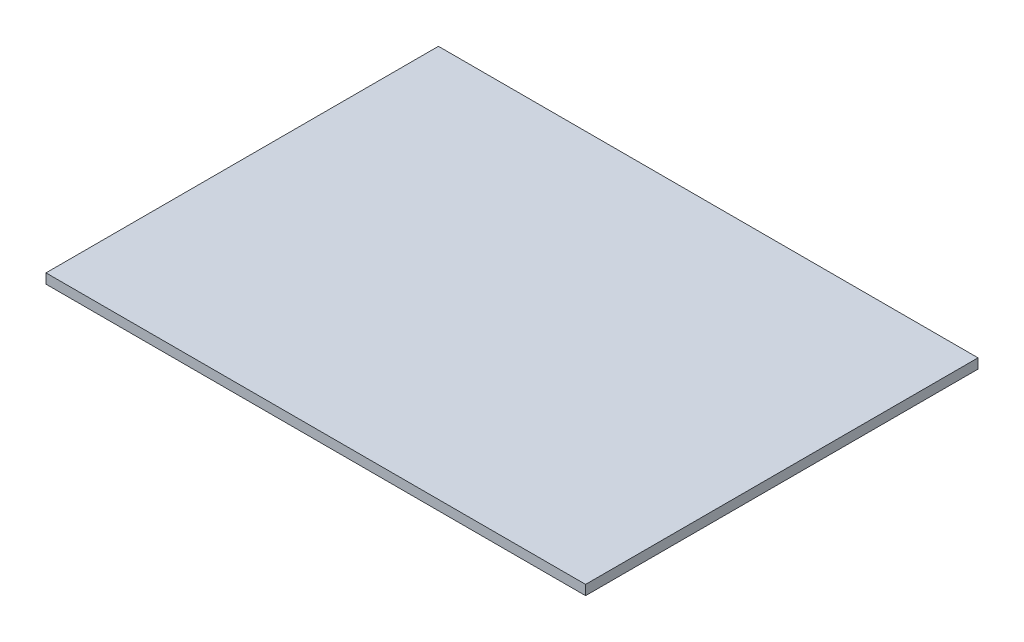
SolidWorks part; units mm, degrees
material "Maple"
ref_plane "Front Plane" through (0, 0, 0) normal (0, 0, 1) x (1, 0, 0)
ref_plane "Top Plane" through (0, 0, 0) normal (0, 1, 0) x (1, 0, 0)
ref_plane "Right Plane" through (0, 0, 0) normal (1, 0, 0) x (0, 0, -1)
sketch "Sketch1" plane through (0, 0, 0) normal (0, 1, 0) x (1, 0, 0)
  line L2 (-400, 300) -> (425, 300)
  line L3 (425, 300) -> (425, -300)
  line L4 (425, -300) -> (-400, -300)
  line L5 (-400, -300) -> (-400, 300)
extrude "Boss-Extrude1" add sketch "Sketch1" along normal blind 15 contours L5 L2 L3 L4
